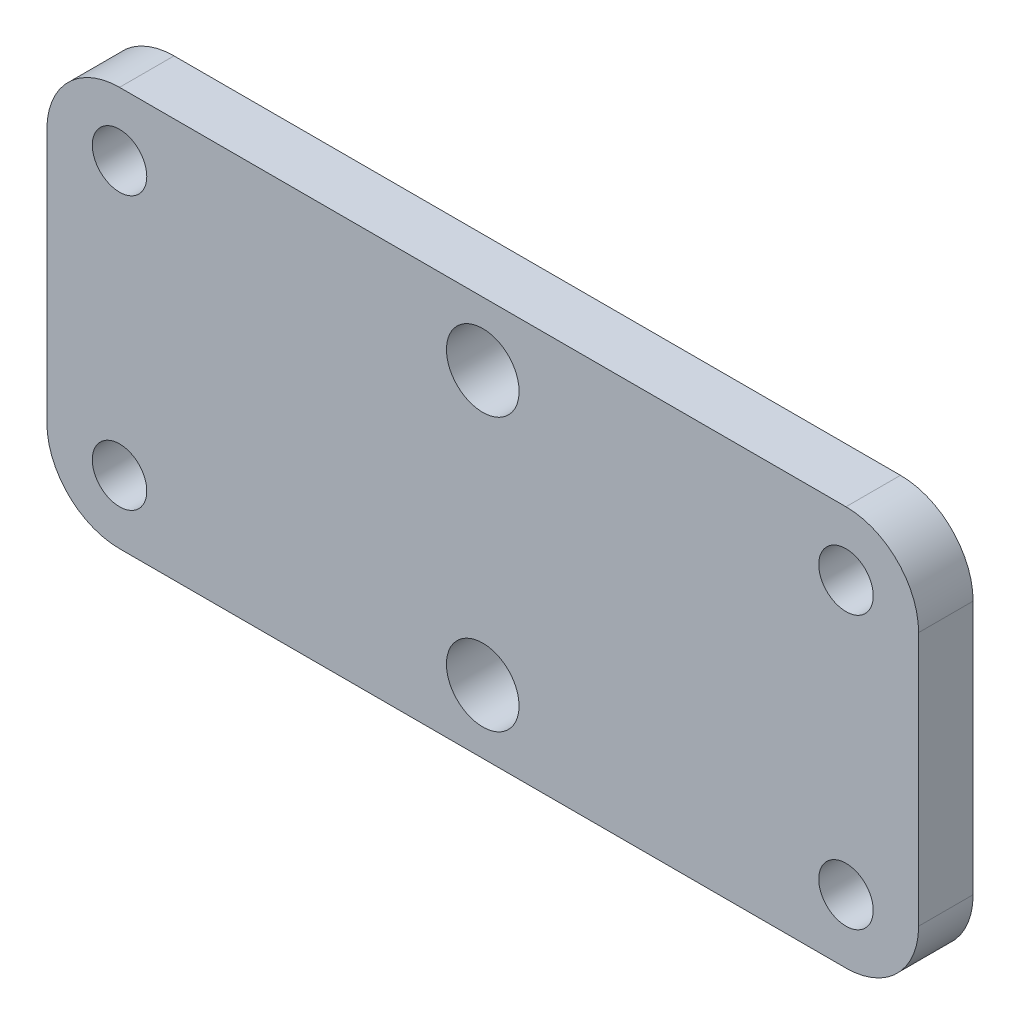
SolidWorks part; units mm, degrees
ref_plane "Plan de face" through (0, 0, 0) normal (0, 0, 1) x (1, 0, 0)
ref_plane "Plan de dessus" through (0, 0, 0) normal (0, 1, 0) x (1, 0, 0)
ref_plane "Plan de droite" through (0, 0, 0) normal (1, 0, 0) x (0, 0, -1)
sketch "Esquisse1" plane through (0, 0, 0) normal (0, 0, 1) x (1, 0, 0)
  line L0 (24, 0) -> (24, -22) construction
  line L1 (0, 0) -> (48, 0)
  line L2 (0, 0) -> (0, -22)
  line L3 (0, -22) -> (48, -22)
  line L4 (48, 0) -> (48, -22)
  line L5 (0, -11) -> (48, -11) construction
  circle A0 centre (24, -3.5) radius 2
  circle A1 centre (24, -18.5) radius 2
  circle A2 centre (4, -3.5) radius 1.5
  circle A3 centre (44, -3.5) radius 1.5
  circle A4 centre (44, -18.5) radius 1.5
  circle A5 centre (4, -18.5) radius 1.5
  point P15 (0, 0)
  dimension "D1" = 4
  dimension "D4" = 3
  dimension "D2" = 15
  dimension "D3" = 22
  dimension "D5" = 4
  dimension "D6" = 15
  dimension "D7" = 40
extrude "Boss.-Extru.1" add sketch "Esquisse1" along normal blind 3
fillet "Congé1" radius 4 4 edges at (48, 0, 1.5) (48, -22, 1.5) (0, -22, 1.5) (0, 0, 1.5)
